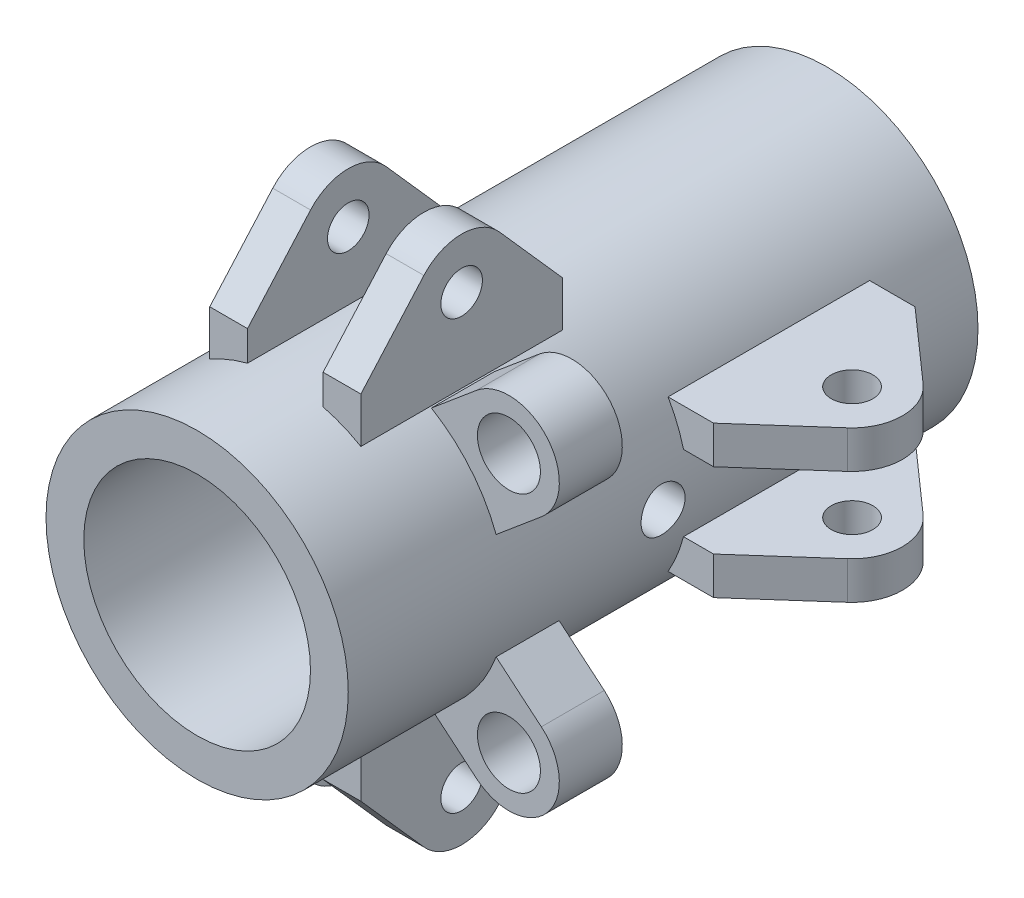
SolidWorks part; units mm, degrees
ref_plane "正面(Front)" through (0, 0, 0) normal (0, 0, 1) x (1, 0, 0)
ref_plane "平面(Top)" through (0, 0, 0) normal (0, 1, 0) x (1, 0, 0)
ref_plane "右側面(Right)" through (0, 0, 0) normal (1, 0, 0) x (0, 0, -1)
sketch "ｽｹｯﾁ1" plane through (0, 0, 0) normal (0, 0, 1) x (1, 0, 0)
  circle A0 centre (0, 0) radius 9
  circle A1 centre (0, 0) radius 12
  dimension "D1" = 18
  dimension "D2" = 24
extrude "ﾎﾞｽ - 押し出し1" add sketch "ｽｹｯﾁ1" along normal blind 50
ref_plane "平面1" through (3, 0, 0) normal (1, 0, 0) x (0, 0, -1)
sketch "ｽｹｯﾁ2" plane through (3, 0, 0) normal (1, 0, 0) x (0, 0, -1)
  line L0 (-43, 9) -> (-43, 14)
  line L1 (-43, 14) -> (-37.9945, 19.652)
  line L2 (-32.0055, 19.652) -> (-27, 14)
  line L3 (-27, 14) -> (-27, 9)
  line L4 (-27, 9) -> (-43, 9)
  line L5 (0, 0) -> (-50, 0) construction
  line L6 (-50, 12) -> (-50, -12) construction
  line L7 (-35, 0) -> (-35, 23.4871) construction
  line L8 (0, 12) -> (-50, 12) construction
  arc A0 (-37.9945, 19.652) -> (-32.0055, 19.652) centre (-35, 17) cw
  circle A2 centre (-35, 17) radius 1.65
  dimension "D2" = 4
  dimension "D3" = 3.3
  dimension "D5" = 5
  dimension "D1" = 9
  dimension "D4" = 5
  dimension "D6" = 16
  dimension "D7" = 15
extrude "ﾎﾞｽ - 押し出し2" add sketch "ｽｹｯﾁ2" along normal blind 3
mirror "ﾐﾗｰ1" about plane through (0, 0, 0) normal (1, 0, 0) of "ﾎﾞｽ - 押し出し2"
sketch "ｽｹｯﾁ3" plane through (0, 0, 0) normal (1, 0, 0) x (0, 0, -1)
  line L0 (0, 0) -> (-50, 0) construction
  line L1 (-50, 12) -> (-50, -12) construction
  circle A0 centre (-25, 0) radius 1.75
  dimension "D1" = 3.5
extrude "ｶｯﾄ - 押し出し1" cut sketch "ｽｹｯﾁ3" against normal through all both and the other way through all
mirror "ﾐﾗｰ2" about plane through (0, 0, 0) normal (0, 1, 0) of "ﾐﾗｰ1", "ﾎﾞｽ - 押し出し2"
ref_plane "平面2" through (0, 3, 0) normal (0, 1, 0) x (1, 0, 0)
sketch "ｽｹｯﾁ5" plane through (0, 3, 0) normal (0, 1, 0) x (1, 0, 0)
  line L0 (0, 0) -> (0, -50) construction
  line L1 (-12, -50) -> (12, -50) construction
  line L2 (9, -7) -> (14, -7)
  line L3 (14, -7) -> (19.652, -12.0055)
  line L4 (19.652, -17.9945) -> (14, -23)
  line L5 (14, -23) -> (9, -23)
  line L6 (9, -23) -> (9, -7)
  line L7 (17, -15) -> (0, -15) construction
  line L8 (12, -23.25) -> (12, 0) construction
  line L9 (9, 0) -> (-9, 0) construction
  arc A0 (19.652, -12.0055) -> (19.652, -17.9945) centre (17, -15) cw
  circle A1 centre (17, -15) radius 1.65
  dimension "D5" = 4
  dimension "D6" = 3.3
  dimension "D1" = 16
  dimension "D2" = 9
  dimension "D3" = 5
  dimension "D4" = 5
  dimension "D7" = 15
extrude "ﾎﾞｽ - 押し出し3" add sketch "ｽｹｯﾁ5" along normal blind 3
mirror "ﾐﾗｰ3" about plane through (0, 0, 0) normal (0, 1, 0) of "ﾎﾞｽ - 押し出し3"
ref_plane "平面3" through (0, 0, 35) normal (0, 0, -1) x (-1, 0, 0)
sketch "ｽｹｯﾁ6" plane through (0, 0, 35) normal (0, 0, -1) x (-1, 0, 0)
  line L0 (-6.0957, 10.3365) -> (-9.6856, 13.3488)
  line L1 (-14.8279, 7.2204) -> (-11.238, 4.2081)
  line L2 (0, 0) -> (-12.2567, 10.2846) construction
  line L3 (-14.8279, 7.2204) -> (-9.6856, 13.3488) construction
  line L4 (0, 0) -> (-32.0823, 0) construction
  line L5 (-11.238, 4.2081) -> (-6.0957, 10.3365)
  arc A0 (-3, 11.619) -> (-6, 10.3923) centre (0, 0) ccw construction
  arc A1 (-9.6856, 13.3488) -> (-14.8279, 7.2204) centre (-12.2567, 10.2846) ccw
  circle A2 centre (0, 0) radius 12 construction
  circle A3 centre (0, 0) radius 12 construction
  circle A4 centre (-12.2567, 10.2846) radius 2.5
  point P16 (-6.0957, 10.3365)
  point P17 (-11.238, 4.2081)
  point P18 (-10.4516, 13.9916)
  dimension "D4" = 5
  dimension "D1" = 40
  dimension "D2" = 8
  dimension "D3" = 4
extrude "ﾎﾞｽ - 押し出し4" add sketch "ｽｹｯﾁ6" along normal mid plane 5
mirror "ﾐﾗｰ4" about plane through (0, 0, 0) normal (0, 1, 0) of "ﾎﾞｽ - 押し出し4"
